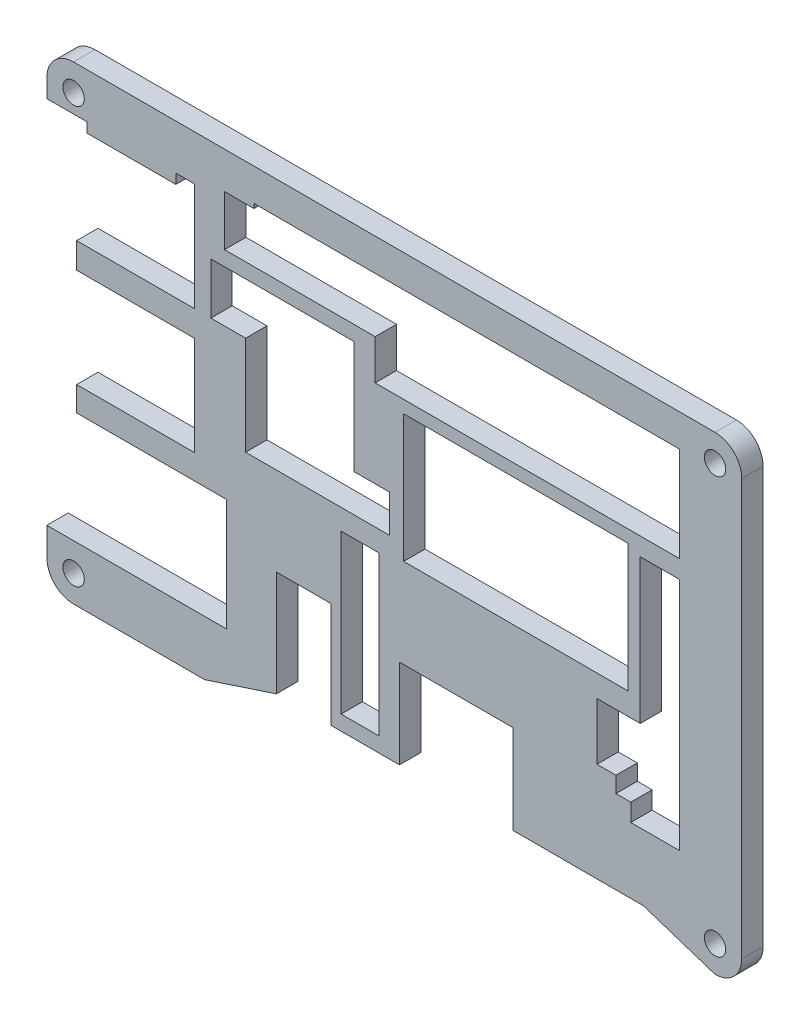
SolidWorks part; units mm, degrees
ref_plane "Front Plane" through (0, 0, 0) normal (0, 0, 1) x (1, 0, 0)
ref_plane "Top Plane" through (0, 0, 0) normal (0, 1, 0) x (1, 0, 0)
ref_plane "Right Plane" through (0, 0, 0) normal (1, 0, 0) x (0, 0, -1)
sketch "Sketch2" plane through (0, 0, 8.1718) normal (0, 0, -1) x (-1, 0, 0)
  line L0 (-23.8449, -33.0844) -> (-34.0849, -36.451) construction
  line L1 (-37.8949, -32.641) -> (-37.8949, 26.6977) construction
  line L2 (-34.0849, 30.5077) -> (57.4049, 30.5077) construction
  line L3 (61.2149, 26.6839) -> (61.2149, 24.0683) construction
  line L4 (56.975, 8.6582) -> (56.975, 4.9979) construction
  line L5 (56.975, -9.1218) -> (56.975, -12.628) construction
  line L6 (61.2149, -28.6278) -> (61.2149, -32.6134) construction
  line L7 (38.7143, -36.451) -> (57.405, -36.451) construction
  line L8 (28.4743, -33.0844) -> (38.7143, -36.451) construction
  line L9 (-23.8449, -33.0844) -> (-34.0849, -36.451)
  line L10 (-37.8949, -32.641) -> (-37.8949, 26.6977)
  line L11 (-34.0849, 30.5077) -> (57.4049, 30.5077)
  line L12 (61.2149, 26.6839) -> (61.2149, 24.0683)
  line L13 (56.975, 8.6582) -> (56.975, 4.9979)
  line L14 (56.975, -9.1218) -> (56.975, -12.628)
  line L15 (61.2149, -28.6278) -> (61.2149, -32.6134)
  line L16 (38.7143, -36.451) -> (57.405, -36.451)
  line L17 (28.4743, -33.0844) -> (38.7143, -36.451)
  line L18 (-23.8449, -33.0844) -> (-5.3029, -33.0844)
  line L19 (-5.3029, -33.0844) -> (-5.3029, -20.3844)
  line L20 (-5.3029, -20.3844) -> (10.9264, -20.3844)
  line L21 (10.9264, -16.0062) -> (10.9264, -22.1276) construction
  line L22 (10.9264, -20.3844) -> (10.9264, -33.0844)
  line L23 (10.9264, -33.0844) -> (20.6581, -33.0844)
  line L24 (20.6581, -33.0844) -> (20.6581, -18.0349)
  line L25 (20.6581, -18.0349) -> (28.4743, -18.0349)
  line L26 (28.4743, -18.0349) -> (28.4743, -33.0844)
  line L27 (13.845, -30.9668) -> (19.2484, -30.9668)
  line L28 (20.6581, -30.9668) -> (13.845, -30.9668) construction
  line L29 (19.2484, -30.9668) -> (19.2484, -8.3602)
  line L30 (19.2484, -8.3602) -> (13.845, -8.3602)
  line L31 (13.845, -8.3602) -> (13.845, -30.9668)
  line L32 (-29.0049, -23.6989) -> (-22.0669, -23.6989) construction
  line L33 (-22.0669, -21.1858) -> (-22.0669, -23.6989) construction
  line L34 (-19.9509, -21.1858) -> (-22.0669, -21.1858) construction
  line L35 (-19.9509, -18.9206) -> (-19.9509, -21.1858) construction
  line L36 (-17.2447, -18.9206) -> (-19.9509, -18.9206) construction
  line L37 (-17.2447, -10.7926) -> (-17.2447, -18.9206) construction
  line L38 (-23.4169, -10.7926) -> (-17.2447, -10.7926) construction
  line L39 (-23.4169, 9.8012) -> (-23.4169, -10.7926) construction
  line L40 (-29.0049, 9.8012) -> (-29.0049, -23.6989) construction
  line L41 (-23.4169, 9.8012) -> (-29.0049, 9.8012) construction
  line L42 (-29.0049, -23.6989) -> (-22.0669, -23.6989)
  line L43 (-22.0669, -21.1858) -> (-22.0669, -23.6989)
  line L44 (-19.9509, -21.1858) -> (-22.0669, -21.1858)
  line L45 (-19.9509, -18.9206) -> (-19.9509, -21.1858)
  line L46 (-17.2447, -18.9206) -> (-19.9509, -18.9206)
  line L47 (-17.2447, -10.7926) -> (-17.2447, -18.9206)
  line L48 (-23.4169, -10.7926) -> (-17.2447, -10.7926)
  line L49 (-23.4169, 9.8012) -> (-23.4169, -10.7926)
  line L50 (-29.0049, 9.8012) -> (-29.0049, -23.6989)
  line L51 (-23.4169, 9.8012) -> (-29.0049, 9.8012)
  line L52 (-21.6389, 10.5941) -> (-21.6389, -7.643) construction
  line L53 (-21.6389, 10.5941) -> (10.329, 10.5941) construction
  line L54 (12.361, -0.0976) -> (17.441, -0.0976) construction
  line L55 (12.361, -0.0976) -> (12.361, -5.4315) construction
  line L56 (37.825, 8.6582) -> (32.872, 8.6582) construction
  line L57 (37.825, 15.9724) -> (37.825, 8.6582) construction
  line L58 (17.441, 15.9724) -> (37.825, 15.9724) construction
  line L59 (17.441, 15.9724) -> (17.441, -0.0976) construction
  line L60 (-21.6389, 10.5941) -> (-21.6389, -7.643)
  line L61 (-21.6389, 10.5941) -> (10.329, 10.5941)
  line L62 (12.361, -0.0976) -> (17.441, -0.0976)
  line L63 (12.361, -0.0976) -> (12.361, -5.4315)
  line L64 (37.825, 8.6582) -> (32.872, 8.6582)
  line L65 (37.825, 15.9724) -> (37.825, 8.6582)
  line L66 (17.441, 15.9724) -> (37.825, 15.9724)
  line L67 (17.441, 15.9724) -> (17.441, -0.0976)
  line L68 (32.872, 8.6582) -> (32.872, -5.4315)
  line L69 (12.361, -5.4315) -> (33.38, -5.4315) construction
  line L70 (32.872, -5.4315) -> (12.361, -5.4315)
  line L71 (-21.6389, -7.643) -> (10.329, -7.643)
  line L72 (10.329, 10.5941) -> (10.329, -9.6302) construction
  line L73 (10.329, -7.643) -> (10.329, 10.5941)
  line L74 (0.6771, 12.3721) -> (-29.0048, 12.3721)
  line L75 (-29.0049, 25.897) -> (-29.0048, 12.0872) construction
  line L76 (-29.0048, 12.3721) -> (-29.0049, 25.897)
  line L77 (-29.0049, 25.897) -> (31.6883, 25.897)
  line L78 (31.6883, 25.897) -> (31.6883, 18.087)
  line L79 (31.6883, 18.087) -> (0.6771, 18.087)
  line L80 (0.6771, 18.087) -> (0.6771, 12.3721)
  line L81 (40.1348, -9.1218) -> (40.1348, 4.9979)
  line L82 (40.1348, 4.9979) -> (56.975, 4.9979)
  line L83 (40.1348, 24.0683) -> (61.2149, 24.0683)
  line L84 (56.975, 8.6582) -> (40.1348, 8.6582)
  line L85 (40.1348, 8.6582) -> (40.1348, 24.0683)
  line L86 (35.285, -9.1218) -> (56.975, -9.1218) construction
  line L87 (40.1348, -9.1218) -> (56.975, -9.1218)
  line L88 (61.2149, -28.6278) -> (35.575, -28.6278)
  line L89 (35.575, -28.6278) -> (35.575, -12.628)
  line L90 (56.975, -12.628) -> (33.9353, -12.628) construction
  line L91 (35.575, -12.628) -> (56.975, -12.628)
  arc A0 (-37.8949, -32.641) -> (-34.0849, -36.451) centre (-34.0849, -32.641) ccw construction
  arc A1 (-34.0849, 30.5077) -> (-37.8949, 26.6977) centre (-34.0849, 26.6977) ccw construction
  arc A2 (61.2149, 26.6839) -> (57.4049, 30.5077) centre (57.4049, 26.6977) ccw construction
  arc A3 (57.405, -36.451) -> (61.2149, -32.6134) centre (57.405, -32.641) ccw construction
  arc A4 (-37.8949, -32.641) -> (-34.0849, -36.451) centre (-34.0849, -32.641) ccw
  arc A5 (-34.0849, 30.5077) -> (-37.8949, 26.6977) centre (-34.0849, 26.6977) ccw
  arc A6 (61.2149, 26.6839) -> (57.4049, 30.5077) centre (57.4049, 26.6977) ccw
  arc A7 (57.405, -36.451) -> (61.2149, -32.6134) centre (57.405, -32.641) ccw
  dimension "D1" = 12.7
  dimension "D2" = 1.4097
  dimension "D3" = 15.0495
  dimension "D4" = 16.8402
  dimension "D5" = 16.8402
extrude "Boss-Extrude1" add sketch "Sketch2" along normal blind 3.048
sketch "Sketch3" plane through (0, 0, 5.1238) normal (0, 0, -1) x (-1, 0, 0)
  circle A0 centre (57.405, -32.641) radius 1.3382
  circle A1 centre (-34.0849, -32.641) radius 1.3382
  circle A2 centre (-34.0849, 26.6977) radius 1.3382
  circle A3 centre (57.4049, 26.6977) radius 1.3382
  dimension "D1" = 2.6765
extrude "Cut-Extrude1" cut sketch "Sketch3" against normal through all
sketch "Sketch4" plane through (0, 0, 5.1238) normal (0, 0, -1) x (-1, 0, 0)
  circle A0 centre (-34.0849, 26.6977) radius 1.524
  circle A1 centre (-34.0849, -32.641) radius 1.524
  circle A2 centre (57.405, -32.641) radius 1.524
  circle A3 centre (57.4049, 26.6977) radius 1.524
  dimension "D1" = 3.048
extrude "Cut-Extrude2" cut sketch "Sketch4" against normal through all
sketch "Sketch5" plane through (0, 0, 5.1238) normal (0, 0, -1) x (-1, 0, 0)
  line L0 (0.6771, 18.087) -> (31.6883, 18.087) construction
  line L1 (14.393, 12.3721) -> (0.6771, 12.3721)
  line L2 (14.393, 12.3721) -> (14.393, 18.087)
  line L3 (14.393, 18.087) -> (0.6771, 18.087)
  line L4 (0.6771, 12.3721) -> (0.6771, 18.087)
  line L5 (31.6883, 25.262) -> (35.88, 25.262)
  line L6 (31.6883, 25.262) -> (31.6883, 18.087)
  line L7 (31.6883, 18.087) -> (35.88, 18.087)
  line L8 (35.88, 25.262) -> (35.88, 18.087)
  line L9 (17.441, 15.9724) -> (17.441, -0.0976) construction
  line L10 (31.6883, 18.087) -> (31.6883, 25.897) construction
  line L11 (35.88, 25.262) -> (37.658, 25.262) construction
  dimension "D1" = 3.048
  dimension "D2" = 4.1917
  dimension "D3" = 7.175
extrude "Cut-Extrude3" cut sketch "Sketch5" against normal through all
sketch "Sketch6" plane through (0, 0, 5.1238) normal (0, 0, -1) x (-1, 0, 0)
  line L0 (61.2149, -28.6278) -> (35.575, -28.6278) construction
  line L1 (55.5253, -27.2308) -> (42.8253, -27.2308)
  line L2 (55.5253, -27.2308) -> (55.5253, -28.6278)
  line L3 (55.5253, -28.6278) -> (42.8253, -28.6278)
  line L4 (42.8253, -27.2308) -> (42.8253, -28.6278)
  line L5 (61.2149, -32.6134) -> (61.2149, -28.6278) construction
  dimension "D1" = 5.6896
  dimension "D2" = 1.397
  dimension "D3" = 12.7
sketch "Sketch7" plane through (0, 0, 5.1238) normal (0, 0, -1) x (-1, 0, 0)
  line L0 (40.1348, 24.0683) -> (61.2149, 24.0683) construction
  line L1 (55.5253, 24.0683) -> (42.8253, 24.0683)
  line L2 (55.5253, 24.0683) -> (55.5253, 22.6713)
  line L3 (55.5253, 22.6713) -> (42.8253, 22.6713)
  line L4 (42.8253, 24.0683) -> (42.8253, 22.6713)
  dimension "D1" = 1.397
  dimension "D2" = 12.7
  dimension "D3" = 5.6896
extrude "Boss-Extrude3" add sketch "Sketch7" against normal blind 3.048
